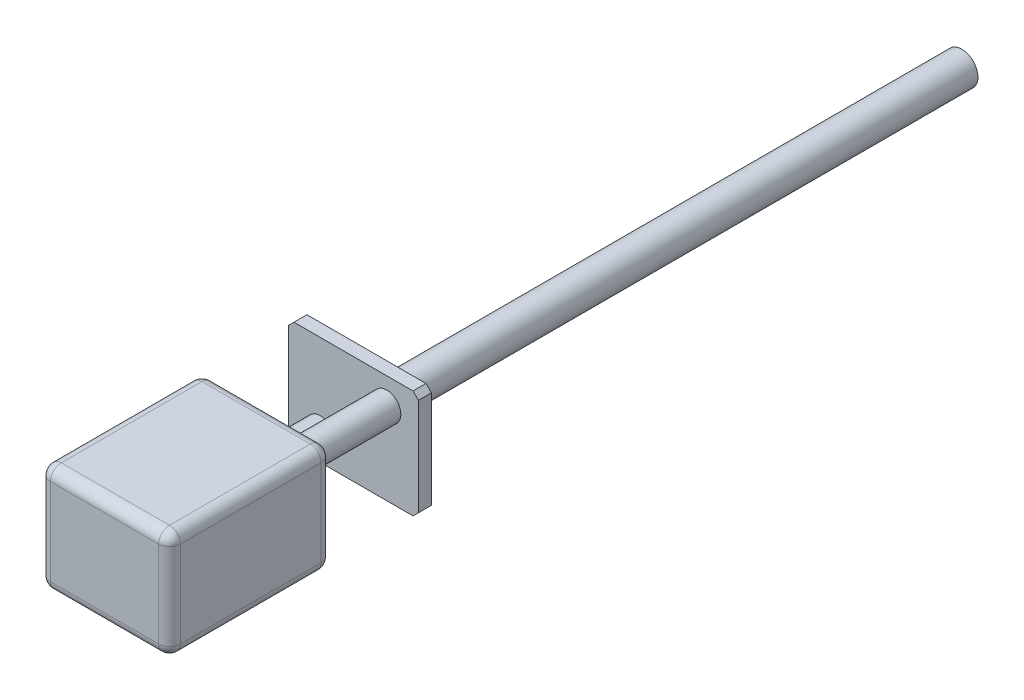
SolidWorks part; units mm, degrees
ref_plane "Front" through (0, 0, 0) normal (0, 0, 1) x (1, 0, 0)
ref_plane "Top" through (0, 0, 0) normal (0, 1, 0) x (1, 0, 0)
ref_plane "Right" through (0, 0, 0) normal (1, 0, 0) x (0, 0, -1)
sketch "草图1" plane through (0, 0, 0) normal (0, 0, 1) x (1, 0, 0)
  line L1 (0, 0) -> (12, 0)
  line L2 (0, 0) -> (0, 10)
  line L3 (0, 10) -> (12, 10)
  line L4 (12, 0) -> (12, 10)
extrude "凸台-拉伸1" add sketch "草图1" along normal blind 15
fillet "圆角1" radius 1 12 edges at (12, 5, 0) (6, 0, 0) (0, 5, 0) (6, 10, 0) (12, 5, 15) (6, 10, 15) (0, 5, 15) (6, 0, 15) (12, 0, 7.5) (0, 0, 7.5) (0, 10, 7.5) (12, 10, 7.5)
sketch "草图2" plane through (0, 0, 0) normal (0, 0, -1) x (-1, 0, 0)
  circle A0 centre (-2.9271, 2.4393) radius 0.8
  circle A1 centre (-9.0729, 7.5607) radius 0.8
  circle A2 centre (-2.9271, 2.4393) radius 1.3
  circle A3 centre (-9.0729, 7.5607) radius 1.3
extrude "凸台-拉伸2" add sketch "草图2" along normal blind 8
sketch "草图3" plane through (0, 0, -8) normal (0, 0, -1) x (-1, 0, 0)
  line L0 (0, 0.5) -> (-0.5, 0)
  line L1 (-0.5, 0) -> (-11.5, 0)
  line L2 (0, 0.5) -> (0, 9.5)
  line L3 (-0.5, 10) -> (-11.5, 10)
  line L4 (-12, 0.5) -> (-12, 9.5)
  line L5 (-11.5, 0) -> (-12, 0.5)
  line L6 (-12, 9.5) -> (-11.5, 10)
  line L7 (0, 9.5) -> (-0.5, 10)
  point P0 (0, 0)
  point P1 (-12, 10)
  point P2 (0, 10)
  point P3 (-12, 0)
extrude "凸台-拉伸3" add sketch "草图3" along normal blind 1.2
sketch "草图6" plane through (0, 0, -9.2) normal (0, 0, -1) x (-1, 0, 0)
  circle A0 centre (-2.9271, 2.4393) radius 0.8
  circle A1 centre (-9.0729, 7.5607) radius 0.8
extrude "切除-拉伸1" cut sketch "草图6" against normal blind 1.2
sketch "草图7" plane through (0, 0, -9.2) normal (0, 0, 1) x (1, 0, 0)
  circle A0 centre (6, 5) radius 1.5
extrude "凸台-拉伸4" add sketch "草图7" against normal blind 55
